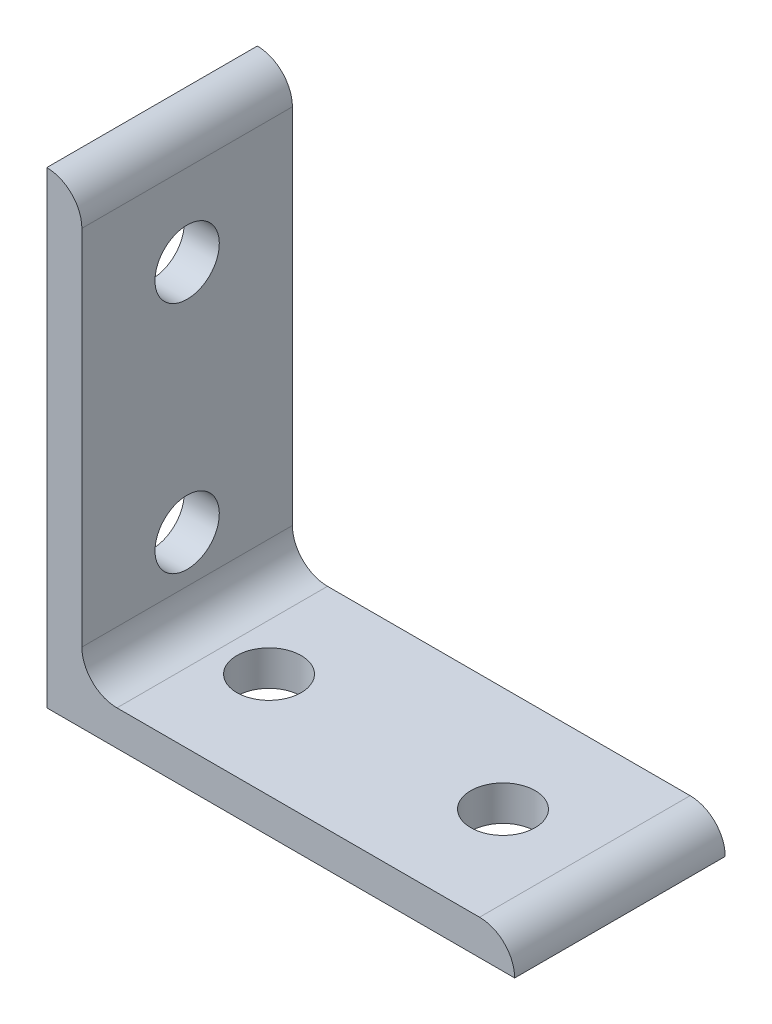
SolidWorks part; units mm, degrees
ref_plane "Front Plane" through (0, 0, 0) normal (0, 0, 1) x (1, 0, 0)
ref_plane "Top Plane" through (0, 0, 0) normal (0, 1, 0) x (1, 0, 0)
ref_plane "Right Plane" through (0, 0, 0) normal (1, 0, 0) x (0, 0, -1)
sketch "Sketch1" plane through (0, 0, 0) normal (0, 0, 1) x (1, 0, 0)
  line L0 (0, 0) -> (0, 40)
  line L1 (3, 37) -> (3, 40) construction
  line L2 (3, 37) -> (3, 6)
  line L3 (6, 3) -> (37, 3)
  line L4 (3, 40) -> (0, 40) construction
  line L5 (40, 0) -> (0, 0)
  line L6 (37, 3) -> (40, 3) construction
  line L7 (40, 3) -> (40, 0) construction
  arc A0 (3, 37) -> (0, 40) centre (0, 37) ccw
  arc A1 (40, 0) -> (37, 3) centre (37, 0) ccw
  arc A2 (3, 6) -> (6, 3) centre (6, 6) ccw
  point P10 (3, 38.5)
  dimension "E" = 3
  dimension "D" = 3
  dimension "C" = 40
  dimension "B" = 40
extrude "Boss-Extrude1" add sketch "Sketch1" along normal mid plane 18
sketch "Sketch2" plane through (0, 0, 0) normal (0, 1, 0) x (1, 0, 0)
  line L0 (0, 0) -> (10, 0) construction
  line L1 (10, 0) -> (30, 0) construction
  circle A0 centre (10, 0) radius 2.75
  circle A1 centre (30, 0) radius 2.75
extrude "Cut-Extrude1" cut sketch "Sketch2" along normal through all
sketch "Sketch3" plane through (0, 0, 0) normal (1, 0, 0) x (0, 0, -1)
  line L0 (0, 0) -> (0, 10) construction
  line L1 (0, 10) -> (0, 30) construction
  circle A0 centre (0, 10) radius 2.75
  circle A1 centre (0, 30) radius 2.75
  dimension "D1" = 10
  dimension "D2" = 20
extrude "Cut-Extrude2" cut sketch "Sketch3" along normal through all
equation "\"E@Sketch3\" = \"E@Sketch2\""
equation "\"D1@Sketch3\" = \"D1@Sketch2\""
equation "\"D2@Sketch3\" = \"D2@Sketch2\""
